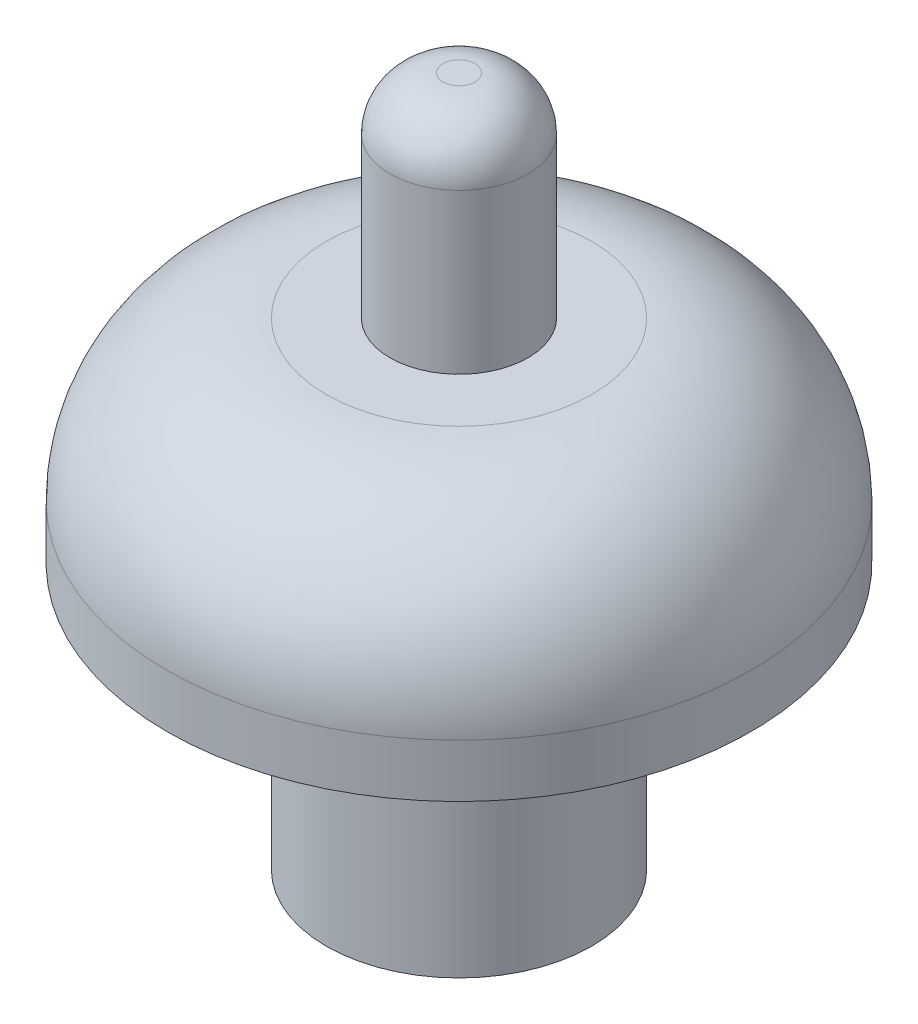
SolidWorks part; units mm, degrees
ref_plane "Ön Düzlem" through (0, 0, 0) normal (0, 0, 1) x (1, 0, 0)
ref_plane "Üst Düzlem" through (0, 0, 0) normal (0, 1, 0) x (1, 0, 0)
ref_plane "Sağ Düzlem" through (0, 0, 0) normal (1, 0, 0) x (0, 0, -1)
sketch "Çizim1" plane through (0, 0, 0) normal (0, 1, 0) x (1, 0, 0)
  circle A0 centre (0, 0) radius 2.5
  circle A1 centre (0, 0) radius 2
  dimension "D1" = 5
extrude "Yükseklik-Ekstrüzyon1" add sketch "Çizim1" along normal blind 9
sketch "Çizim2" plane through (0, 9, 0) normal (0, 1, 0) x (1, 0, 0)
  circle A0 centre (0, 0) radius 5.5
  dimension "D1" = 11
extrude "Yükseklik-Ekstrüzyon2" add sketch "Çizim2" against normal blind 4 separate body
fillet "Radyus1" radius 3 1 edges at (0, 9, 5.5)
sketch "Çizim3" plane through (0, 9, 0) normal (0, 1, 0) x (1, 0, 0)
  circle A0 centre (0, 0) radius 1.3002
extrude "Yükseklik-Ekstrüzyon3" add sketch "Çizim3" along normal blind 4
fillet "Radyus2" radius 1 1 edges at (0, 13, 1.3002)
